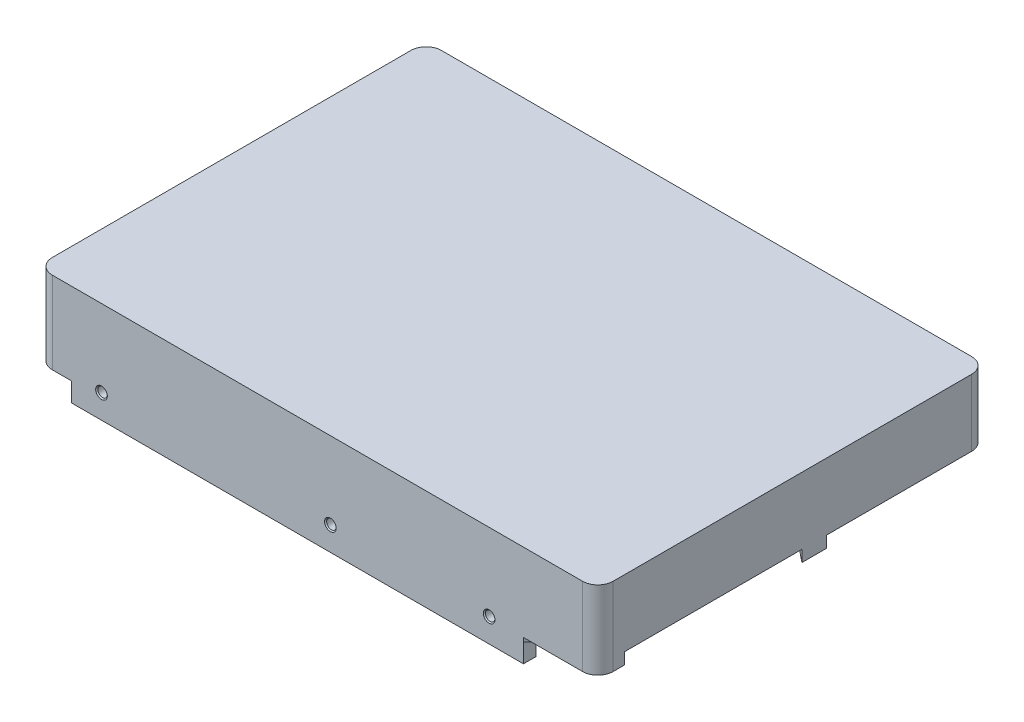
SolidWorks part; units mm, degrees
ref_plane "前视基准面" through (0, 0, 0) normal (0, 0, 1) x (1, 0, 0)
ref_plane "上视基准面" through (0, 0, 0) normal (0, 1, 0) x (1, 0, 0)
ref_plane "右视基准面" through (0, 0, 0) normal (1, 0, 0) x (0, 0, -1)
sketch "草图4" plane through (0, 0, 0) normal (0, 1, 0) x (1, 0, 0)
  line L0 (0, 79.422) -> (0, -78.3018) construction
  line L1 (0, -55) -> (0, 55) construction
  line L2 (-82.6706, 0) -> (70.3484, 0) construction
  line L3 (-55, 0) -> (55, 0) construction
  line L5 (-73.5, 51) -> (73.5, 51)
  line L6 (-73.5, 51) -> (-73.5, -51)
  line L7 (-73.5, -51) -> (73.5, -51)
  line L8 (73.5, 51) -> (73.5, -51)
  dimension "D1" = 147
  dimension "D2" = 102
extrude "凸台-拉伸1" add sketch "草图4" along normal blind 26.5
hole_wizard "M3 螺纹孔2" positions "草图8" profile "草图9" tap size "M3" standard "GB"
sketch "草图8" plane through (0, 0, 0) normal (0, -1, 0) x (-1, 0, 0)
  line L0 (-73.5, -51) -> (-73.5, 51) construction
  line L4 (-14.575, 0) -> (14.575, 0) construction
  point P0 (-32.22, -47.5)
  dimension "D1" = 41.28
  dimension "D2" = 47.5
sketch "草图9" plane through (32.22, 0, 47.5) normal (1, 0, 0) x (0, 0, -1)
  line L0 (0, 0) -> (0, 8.2511)
  line L1 (0, 8.2511) -> (1.25, 7.5)
  line L2 (1.25, 7.5) -> (1.25, 0.275)
  line L3 (1.25, 0.275) -> (1.525, 0)
  line L5 (1.525, 0) -> (0, 0)
  line L6 (-1.25, 0.275) -> (-1.525, 0) construction
  line L10 (0, 8.2511) -> (-1.25, 7.5) construction
  line L11 (0, -6.35) -> (0, 107.95) construction
  dimension "螺纹孔钻头直径" = 2.5
  dimension "螺纹孔钻头深度" = 7.5
  dimension "近端锥形沉头孔直径" = 3.05
  dimension "近端锥形沉头孔角度" = 90
  dimension "导头角度" = 118
cosmetic thread "孔螺蚊线2" parameters "D1"=6, "D2"=3
pattern_linear "阵列(线性)3" count 2 spacing 44.45 along (-1, 0, 0) count 2 spacing 95 along (0, 0, -1) of "M3 螺纹孔2"
sketch "草图10" plane through (0, 0, 51) normal (0, 0, 1) x (1, 0, 0)
  line L1 (-73.5, 0) -> (-64.5, 0)
  line L2 (-73.5, 0) -> (-73.5, 5)
  line L3 (-73.5, 5) -> (-64.5, 5)
  line L4 (-64.5, 0) -> (-64.5, 5)
  dimension "D1" = 9
  dimension "D2" = 5
extrude "切除-拉伸1" cut sketch "草图10" against normal through all
sketch "草图12" plane through (0, 0, 51) normal (0, 0, 1) x (1, 0, 0)
  line L1 (73.5, 0) -> (54, 0)
  line L2 (73.5, 0) -> (73.5, 5)
  line L3 (73.5, 5) -> (54, 5)
  line L4 (54, 0) -> (54, 5)
  dimension "D1" = 19.5
  dimension "D2" = 5
extrude "切除-拉伸2" cut sketch "草图12" against normal through all
sketch "草图13" plane through (0, 5, 0) normal (0, -1, 0) x (1, 0, 0)
  line L0 (54, -51) -> (73.5, -31.5)
  line L1 (73.5, -51) -> (73.5, 51) construction
  line L2 (73.5, -31.5) -> (73.5, -51)
  line L3 (73.5, -51) -> (54, -51)
  line L4 (73.5, -51) -> (54, -51) construction
  dimension "D1" = 45
extrude "切除-拉伸3" cut sketch "草图13" against normal blind 4
sketch "草图14" plane through (0, 5, 0) normal (0, -1, 0) x (1, 0, 0)
  line L0 (54, 51) -> (73.5, 31.5)
  line L1 (73.5, -31.5) -> (73.5, 51) construction
  line L2 (73.5, 31.5) -> (73.5, 51)
  line L3 (73.5, 51) -> (54, 51)
  dimension "D1" = 45
extrude "切除-拉伸4" cut sketch "草图14" against normal blind 1
sketch "草图15" plane through (0, 0, 0) normal (0, -1, 0) x (1, 0, 0)
  line L1 (54, -51) -> (54, 51) construction
  line L2 (54, 47.7) -> (35.7143, 47.7)
  line L3 (-64.5, -51) -> (-64.5, 51) construction
  line L4 (-64.5, 47.7) -> (-64.5, -47.7)
  line L5 (-64.5, -51) -> (-64.5, 51) construction
  line L6 (-64.5, -47.7) -> (-15.7243, -47.7)
  line L7 (54, -51) -> (54, 51) construction
  line L8 (54, -47.7) -> (54, 47.7)
  line L9 (-77.941, 0) -> (64.9096, 0) construction
  line L10 (14.575, 0) -> (-14.575, 0) construction
  line L12 (-64.5, 51) -> (54, 51) construction
  line L13 (28.7257, 47.7) -> (-8.7357, 47.7)
  line L14 (-15.7243, 47.7) -> (-64.5, 47.7)
  line L15 (35.7143, -47.7) -> (54, -47.7)
  line L16 (-8.7357, -47.7) -> (28.7257, -47.7)
  arc A0 (28.7257, 47.7) -> (35.7143, 47.7) centre (32.22, 47.5) ccw
  arc A1 (-15.7243, 47.7) -> (-8.7357, 47.7) centre (-12.23, 47.5) ccw
  arc A2 (35.7143, -47.7) -> (28.7257, -47.7) centre (32.22, -47.5) ccw
  arc A3 (-8.7357, -47.7) -> (-15.7243, -47.7) centre (-12.23, -47.5) ccw
  dimension "D2" = 7
  dimension "D1" = 3.3
extrude "切除-拉伸7" cut sketch "草图15" against normal blind 5
sketch "草图16" plane through (0, 5, 0) normal (0, -1, 0) x (1, 0, 0)
  line L0 (54, 47.7) -> (35.7143, 47.7) construction
  line L1 (42, 47.7) -> (48, 47.7)
  line L2 (42, 47.7) -> (42, 44.7)
  line L3 (42, 44.7) -> (48, 44.7)
  line L4 (48, 47.7) -> (48, 44.7)
  line L5 (45, 47.7) -> (45, 41.8386) construction
  line L6 (73.5, 31.5) -> (73.5, 51) construction
  dimension "D1" = 3
  dimension "D2" = 6
  dimension "D3" = 28.5
extrude "切除-拉伸8" cut sketch "草图16" against normal blind 4
pattern_linear "阵列(线性)4" count 2 spacing 41.61 along (-1, 0, 0) count 2 spacing 101.6 along (-1, 0, 0) of "切除-拉伸8"
mirror "镜向2" about plane through (0, 0, 0) normal (0, 0, 1) of "阵列(线性)4", "切除-拉伸8"
hole_wizard "M3 螺纹孔1" positions "草图5" profile "草图7" tap size "M3" standard "GB"
sketch "草图5" plane through (0, 0, 51) normal (0, 0, 1) x (1, 0, 0)
  line L0 (73.5, 26.5) -> (73.5, 6) construction
  line L2 (-64.5, 0) -> (54, 0) construction
  point P0 (45, 6.25)
  dimension "D1" = 28.5
  dimension "D2" = 6.25
sketch "草图7" plane through (45, 6.25, 51) normal (1, 0, 0) x (0, -1, 0)
  line L0 (0, 0) -> (0, 5.7511)
  line L1 (0, 5.7511) -> (1.25, 5)
  line L2 (1.25, 5) -> (1.25, 0.275)
  line L3 (1.25, 0.275) -> (1.525, 0)
  line L5 (1.525, 0) -> (0, 0)
  line L6 (-1.25, 0.275) -> (-1.525, 0) construction
  line L10 (0, 5.7511) -> (-1.25, 5) construction
  line L11 (0, -6.35) -> (0, 107.95) construction
  dimension "螺纹孔钻头直径" = 2.5
  dimension "螺纹孔钻头深度" = 5
  dimension "近端锥形沉头孔直径" = 3.05
  dimension "近端锥形沉头孔角度" = 90
  dimension "导头角度" = 118
cosmetic thread "孔螺蚊线3" parameters "D1"=3.3, "D2"=3
pattern_linear "阵列(线性)1" count 2 spacing 41.61 along (-1, 0, 0) count 2 spacing 101.6 along (-1, 0, 0) of "M3 螺纹孔1"
mirror "镜向4" about plane through (0, 0, 0) normal (0, 0, 1) of "阵列(线性)1", "M3 螺纹孔1"
sketch "草图17" plane through (0, 5, 0) normal (0, -1, 0) x (1, 0, 0)
  line L1 (73.5, 51) -> (54, 51) construction
  line L3 (73.5, -31.5) -> (73.5, 31.5) construction
  circle A0 centre (57, 44) radius 2.5
  dimension "D1" = 5
  dimension "D3" = 7
  dimension "D2" = 16.5
extrude "凸台-拉伸2" add sketch "草图17" along normal blind 3
pattern_linear "阵列(线性)5" count 2 spacing 46.5 along (-1, 0, 0) of "凸台-拉伸2"
sketch "草图18" plane through (0, 5, 0) normal (0, -1, 0) x (1, 0, 0)
  line L0 (73.5, -31.5) -> (73.5, 31.5) construction
  line L1 (59, -16) -> (30.8131, -16) construction
  line L2 (10.5, 44) -> (10.5, -41.132) construction
  circle A0 centre (10.5, -30) radius 2.5
  circle A1 centre (42.5, -16) radius 2.5
  circle A2 centre (59, -16) radius 2.5
  circle A3 centre (17, 9.5) radius 2.5
  circle A4 centre (57, 44) radius 2.5 construction
  circle A5 centre (10.5, 44) radius 2.5 construction
  circle A6 centre (57, 44) radius 2.5 construction
  dimension "D1" = 74
  dimension "D2" = 34.5
  dimension "D3" = 16.5
  dimension "D4" = 60
  dimension "D6" = 56.5
  dimension "D5" = 14.5
extrude "凸台-拉伸3" add sketch "草图18" along normal blind 3
draft "拔模1" type of draft neutral plane draft angle 2 faces to draft 6 face at (10.5, 2, -32.5) face at (59, 2, -18.5) face at (42.5, 2, -18.5) face at (17, 2, 7) face at (10.5, 2, 41.5) face at (57, 2, 41.5) neutral plane through (-73.5, 5, -51) neutral plane normal (0, -1, 0) parameters "D1"=2
sketch "草图19" plane through (0, 5, 0) normal (0, -1, 0) x (1, 0, 0)
  line L7 (54, 51) -> (73.5, 31.5) construction
  line L8 (64.5, 40.5) -> (73.5, 40.5)
  line L9 (64.5, 40.5) -> (64.5, -40.5)
  line L10 (64.5, -40.5) -> (73.5, -40.5)
  line L11 (73.5, 40.5) -> (73.5, -40.5)
  line L12 (73.5, -51) -> (73.5, -31.5) construction
  line L13 (73.5, -31.5) -> (54, -51) construction
  dimension "D1" = 9
extrude "切除-拉伸9" cut sketch "草图19" against normal blind 1
sketch "草图21" plane through (0, 5, 0) normal (0, -1, 0) x (1, 0, 0)
  line L0 (64.5, 40.5) -> (64.5, -40.5) construction
  line L1 (73.5, -51) -> (64.5, -51)
  line L2 (73.5, -51) -> (73.5, -9)
  line L3 (73.5, -9) -> (64.5, -9)
  line L4 (64.5, -51) -> (64.5, -9)
  line L5 (73.5, -31.5) -> (73.5, 51) construction
  line L6 (73.5, 44) -> (69.5, 44)
  line L7 (73.5, 44) -> (73.5, -2.5)
  line L9 (64.5, 44) -> (64.5, -2.4793)
  line L10 (64.5, 40.5) -> (64.5, -40.5) construction
  line L11 (73.5, 51) -> (54, 51) construction
  line L12 (69.5, -1.2947) -> (69.5, -6.7582) construction
  line L17 (66, 44) -> (64.5, 44)
  line L19 (66, 44) -> (66, 47.3875)
  line L20 (66, 47.3875) -> (69.5, 47.3875)
  line L21 (69.5, 44) -> (69.5, 47.3875)
  line L23 (71, -5.5) -> (71, -4.5)
  line L24 (71, -4.5) -> (73.5, -2.5)
  line L25 (68, -5.5) -> (68, -4.5)
  line L26 (68, -4.5) -> (64.5, -2.4793)
  arc A1 (68, -5.5) -> (71, -5.5) centre (69.5, -5.5) ccw
  dimension "D4" = 4
  dimension "D10" = 1.5
  dimension "D1" = 42
  dimension "D2" = 7
  dimension "D3" = 46.5
  dimension "D5" = 3.5
  dimension "D6" = 1
  dimension "D7" = 4
  dimension "D8" = 3.5
  dimension "D9" = 3.6125
  dimension "D11" = 120
extrude "切除-拉伸10" cut sketch "草图21" along direction (0, -1, 0) on the side against the normal up to surface (4 mm away)
sketch "草图22" plane through (0, 9, 0) normal (0, -1, 0) x (1, 0, 0)
  line L0 (73.5, 44) -> (73.5, -2.5) construction
  line L1 (64.5, 44) -> (71.5, 44)
  line L2 (64.5, 44) -> (64.5, 3)
  line L3 (64.5, 3) -> (71.5, 3)
  line L4 (71.5, 44) -> (71.5, 3)
  line L5 (54, -51) -> (73.5, -51) construction
  line L6 (64.5, -9) -> (71.5, -9)
  line L7 (64.5, -9) -> (64.5, -49.5)
  line L8 (64.5, -49.5) -> (71.5, -49.5)
  line L9 (71.5, -9) -> (71.5, -49.5)
  dimension "D1" = 2
  dimension "D2" = 41
  dimension "D3" = 1.5
extrude "切除-拉伸11" cut sketch "草图22" against normal blind 6
hole_wizard "M3 螺纹孔3" positions "草图23" profile "草图24" tap size "M3" standard "GB"
sketch "草图23" plane through (0, 2, 0) normal (0, -1, 0) x (-1, 0, 0)
  point P0 (-57, -44)
  point P4 (-10.5, -44)
  point P7 (-17, -9.5)
  point P10 (-10.5, 30)
  point P13 (-42.5, 16)
  point P16 (-59, 16)
sketch "草图24" plane through (57, 2, 44) normal (1, 0, 0) x (0, 0, -1)
  line L0 (0, 0) -> (0, 9.2511)
  line L1 (0, 9.2511) -> (1.25, 8.5)
  line L2 (1.25, 8.5) -> (1.25, 0.275)
  line L3 (1.25, 0.275) -> (1.525, 0)
  line L5 (1.525, 0) -> (0, 0)
  line L6 (-1.25, 0.275) -> (-1.525, 0) construction
  line L10 (0, 9.2511) -> (-1.25, 8.5) construction
  line L11 (0, -6.35) -> (0, 107.95) construction
  dimension "螺纹孔钻头直径" = 2.5
  dimension "螺纹孔钻头深度" = 8.5
  dimension "近端锥形沉头孔直径" = 3.05
  dimension "近端锥形沉头孔角度" = 90
  dimension "导头角度" = 118
cosmetic thread "孔螺蚊线4" parameters "D1"=6, "D2"=3
cosmetic thread "孔螺蚊线5" parameters "D1"=6, "D2"=3
cosmetic thread "孔螺蚊线6" parameters "D1"=6, "D2"=3
cosmetic thread "孔螺蚊线7" parameters "D1"=6, "D2"=3
cosmetic thread "孔螺蚊线8" parameters "D1"=6, "D2"=3
cosmetic thread "孔螺蚊线9" parameters "D1"=6, "D2"=3
fillet "圆角1" radius 4 4 edges at (-73.5, 15.75, -51) (-73.5, 15.75, 51) (73.5, 16.25, 51) (73.5, 17.75, -51)
